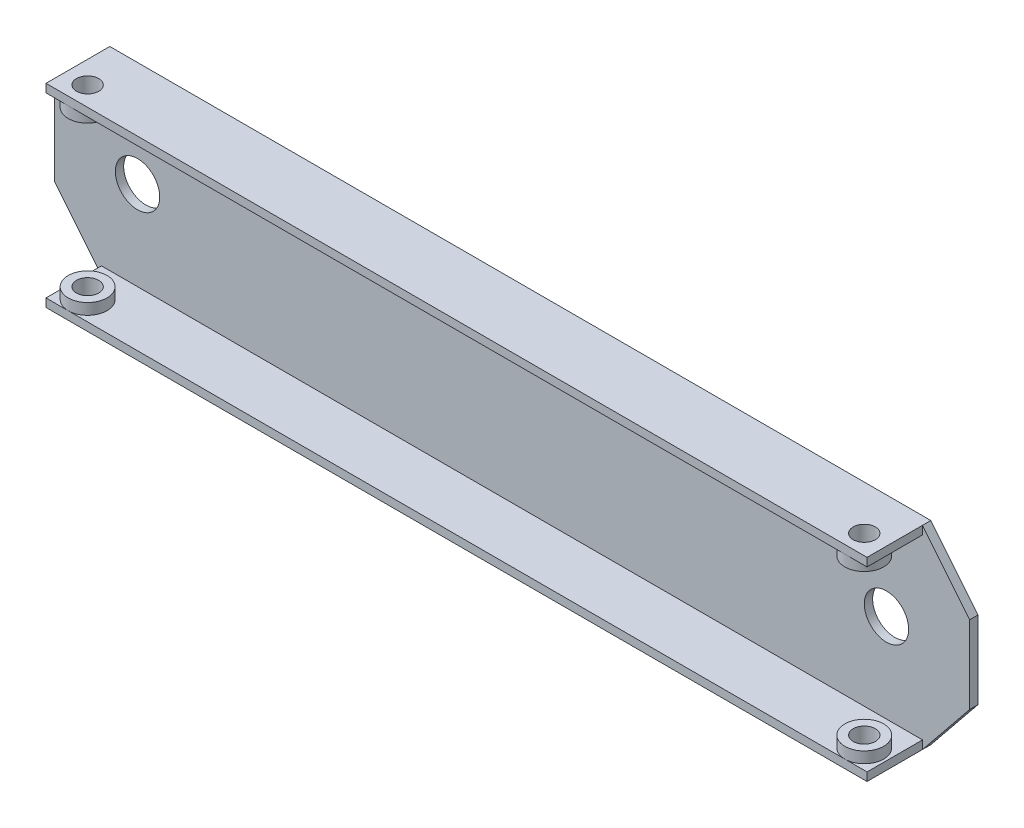
SolidWorks part; units mm, degrees
ref_plane "Alzado" through (0, 0, 0) normal (0, 0, 1) x (1, 0, 0)
ref_plane "Planta" through (0, 0, 0) normal (0, 1, 0) x (1, 0, 0)
ref_plane "Vista lateral" through (0, 0, 0) normal (1, 0, 0) x (0, 0, -1)
sketch "Croquis1" plane through (0, 0, 0) normal (0, 0, 1) x (1, 0, 0)
  line L0 (110.115, 26.8069) -> (118.615, 16.3069)
  line L1 (-37.885, 26.8069) -> (110.115, 26.8069)
  line L2 (36.115, 26.8069) -> (36.115, -8.1931) construction
  line L3 (-37.885, -8.1931) -> (110.115, -8.1931)
  line L4 (-46.385, 2.3069) -> (-37.885, -8.1931)
  line L5 (118.615, 16.3069) -> (118.615, 2.3069)
  line L6 (118.615, 2.3069) -> (110.115, -8.1931)
  line L7 (-46.385, 16.3069) -> (-46.385, 2.3069)
  line L8 (-37.885, 26.8069) -> (-46.385, 16.3069)
  dimension "D2" = 8.5
  dimension "D1" = 14
  dimension "D3" = 8.5
  dimension "D4" = 10.5
  dimension "D5" = 10.5
  dimension "D6" = 165
extrude "Saliente-Extruir1" add sketch "Croquis1" along normal blind 1.5
sketch "Croquis4" plane through (0, 0, 1.5) normal (0, 0, 1) x (1, 0, 0)
  line L0 (-37.885, 26.8069) -> (-37.885, 25.3069)
  line L1 (-37.885, 25.3069) -> (110.115, 25.3069)
  line L2 (110.115, 25.3069) -> (110.115, 26.8069)
  line L3 (110.115, 26.8069) -> (-37.885, 26.8069)
  dimension "D1" = 1.5
extrude "Saliente-Extruir2" add sketch "Croquis4" along normal blind 10
sketch "Croquis5" plane through (0, 0, 1.5) normal (0, 0, 1) x (1, 0, 0)
  line L0 (-37.885, -8.1931) -> (-37.885, -6.6931)
  line L1 (-37.885, -6.6931) -> (110.115, -6.6931)
  line L2 (110.115, -6.6931) -> (110.115, -8.1931)
  line L3 (110.115, -8.1931) -> (-37.885, -8.1931)
  dimension "D1" = 1.5
extrude "Saliente-Extruir3" add sketch "Croquis5" along normal blind 10
sketch "Croquis6" plane through (0, 26.8069, 0) normal (0, 1, 0) x (1, 0, 0)
  line L0 (110.115, -11.5) -> (110.115, -1.5) construction
  line L2 (110.115, 0) -> (-37.885, 0) construction
  line L3 (-37.885, -11.5) -> (-37.885, -1.5) construction
  circle A0 centre (106.115, -8) radius 2
  circle A1 centre (-33.885, -8) radius 2
  dimension "D1" = 4
  dimension "D4" = 4
  dimension "D2" = 4
  dimension "D3" = 8
  dimension "D5" = 8
  dimension "D6" = 4
extrude "Cortar-Extruir6" cut sketch "Croquis6" against normal blind 3.5
sketch "Croquis9" plane through (0, 25.3069, 0) normal (0, -1, 0) x (1, 0, 0)
  circle A0 centre (-33.885, 8) radius 3.5
extrude "Saliente-Extruir5" add sketch "Croquis9" along normal blind 2
sketch "Croquis11" plane through (0, 23.3069, 0) normal (0, -1, 0) x (1, 0, 0)
  circle A0 centre (-33.885, 8) radius 2
  dimension "D1" = 4
extrude "Cortar-Extruir7" cut sketch "Croquis11" against normal blind 2
sketch "Croquis12" plane through (0, 25.3069, 0) normal (0, -1, 0) x (1, 0, 0)
  circle A0 centre (106.115, 8) radius 3.5
extrude "Saliente-Extruir6" add sketch "Croquis12" along normal blind 2
sketch "Croquis13" plane through (0, 23.3069, 0) normal (0, -1, 0) x (1, 0, 0)
  circle A0 centre (106.115, 8) radius 2
extrude "Cortar-Extruir8" cut sketch "Croquis13" against normal blind 2
sketch "Croquis14" plane through (0, -8.1931, 0) normal (0, -1, 0) x (1, 0, 0)
  line L0 (-37.885, 0) -> (110.115, 0) construction
  line L1 (-37.885, 11.5) -> (-37.885, 1.5) construction
  circle A0 centre (-33.885, 8) radius 2
  dimension "D1" = 8
  dimension "D3" = 4
  dimension "D2" = 4
extrude "Cortar-Extruir9" cut sketch "Croquis14" against normal up to next
sketch "Croquis15" plane through (0, -6.6931, 0) normal (0, 1, 0) x (1, 0, 0)
  circle A0 centre (-33.885, -8) radius 3.5
extrude "Saliente-Extruir7" add sketch "Croquis15" along normal blind 2
sketch "Croquis16" plane through (0, -4.6931, 0) normal (0, 1, 0) x (1, 0, 0)
  circle A0 centre (-33.885, -8) radius 2
extrude "Cortar-Extruir10" cut sketch "Croquis16" against normal blind 2
sketch "Croquis17" plane through (0, -8.1931, 0) normal (0, -1, 0) x (1, 0, 0)
  line L0 (110.115, 11.5) -> (110.115, 1.5) construction
  line L1 (-37.885, 0) -> (110.115, 0) construction
  circle A0 centre (106.115, 8) radius 2
  dimension "D1" = 4
  dimension "D2" = 4
  dimension "D3" = 8
extrude "Cortar-Extruir11" cut sketch "Croquis17" against normal up to next
sketch "Croquis18" plane through (0, -6.6931, 0) normal (0, 1, 0) x (1, 0, 0)
  circle A0 centre (106.115, -8) radius 3.5
extrude "Saliente-Extruir8" add sketch "Croquis18" along normal blind 2
sketch "Croquis19" plane through (0, -4.6931, 0) normal (0, 1, 0) x (1, 0, 0)
  circle A0 centre (106.115, -8) radius 2
extrude "Cortar-Extruir12" cut sketch "Croquis19" against normal blind 2
sketch "Croquis20" plane through (0, 0, 1.5) normal (0, 0, 1) x (1, 0, 0)
  line L0 (-46.385, 16.3069) -> (-46.385, 2.3069) construction
  line L1 (118.615, 2.3069) -> (118.615, 16.3069) construction
  line L2 (110.115, 26.8069) -> (-37.885, 26.8069) construction
  line L3 (-37.885, -8.1931) -> (110.115, -8.1931) construction
  circle A0 centre (-31.385, 9.3069) radius 4
  circle A1 centre (103.615, 9.3069) radius 4
  dimension "D1" = 15
  dimension "D2" = 8
  dimension "D3" = 15
  dimension "D4" = 17.5
  dimension "D5" = 17.5
extrude "Cortar-Extruir13" cut sketch "Croquis20" against normal up to next
